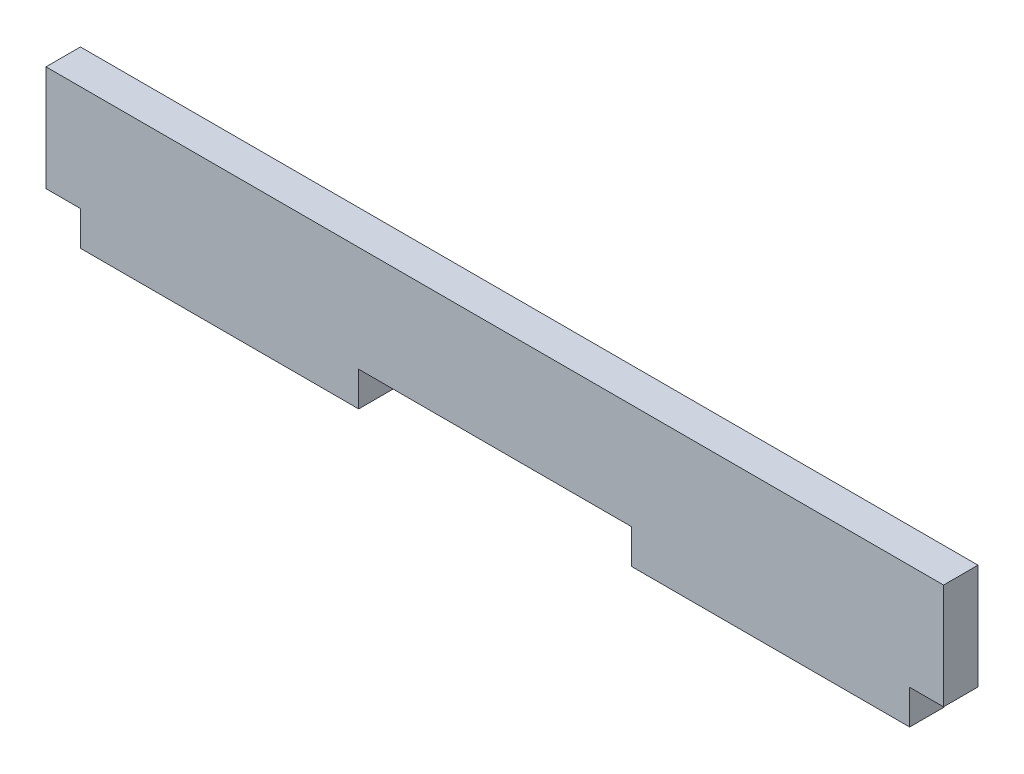
SolidWorks part; units mm, degrees
ref_plane "Front Plane" through (0, 0, 0) normal (0, 0, 1) x (1, 0, 0)
ref_plane "Top Plane" through (0, 0, 0) normal (0, 1, 0) x (1, 0, 0)
ref_plane "Right Plane" through (0, 0, 0) normal (1, 0, 0) x (0, 0, -1)
sketch "Sketch1" plane through (0, 0, 0) normal (0, 0, 1) x (1, 0, 0)
  line L0 (-12.6492, -4.7625) -> (12.7, -4.7625)
  line L1 (-41.275, 4.7625) -> (41.275, 4.7625)
  line L2 (-41.275, 4.7625) -> (-41.275, -4.7625)
  line L3 (-41.275, -4.7625) -> (-38.1, -4.7625)
  line L4 (41.275, 4.7625) -> (41.275, -4.7625)
  line L5 (-41.275, 4.7625) -> (41.275, -4.7625) construction
  line L6 (-41.275, -4.7625) -> (41.275, 4.7625) construction
  line L8 (-12.6492, -4.7625) -> (-12.6492, -7.9375)
  line L9 (-12.6492, -7.9375) -> (-38.1, -7.9375)
  line L10 (-38.1, -4.7625) -> (-38.1, -7.9375)
  line L12 (12.7, -4.7625) -> (12.7, -7.9375)
  line L13 (12.7, -7.9375) -> (38.1508, -7.9375)
  line L14 (38.1508, -4.7625) -> (38.1508, -7.9375)
  line L15 (38.1508, -4.7625) -> (41.275, -4.7625)
  point P0 (0, 0)
  point P14 (25.4254, -7.9375)
  point P15 (-25.3746, -7.9375)
  dimension "D1" = 9.525
  dimension "D2" = 82.55
  dimension "D3" = 3.175
  dimension "D4" = 25.4508
  dimension "D5" = 50.8
  dimension "D6" = 25.4508
  dimension "D7" = 12.7
extrude "Boss-Extrude1" add sketch "Sketch1" along normal mid plane 3.175
ref_plane "Plane1" through (0, 0, 1.5875) normal (0, 0, 1) x (1, 0, 0)
sketch "Sketch2" plane through (0, 0, 1.5875) normal (0, 0, 1) x (1, 0, 0)
  line L24 (38.2524, -4.8641) -> (41.3766, -4.8641)
  line L25 (41.3766, -4.8641) -> (41.3766, 4.8641)
  line L26 (41.3766, 4.8641) -> (-41.3766, 4.8641)
  line L27 (-41.3766, 4.8641) -> (-41.3766, -4.8641)
  line L28 (-41.3766, -4.8641) -> (-38.2016, -4.8641)
  line L29 (-38.2016, -4.8641) -> (-38.2016, -8.0391)
  line L30 (-38.2016, -8.0391) -> (-12.5476, -8.0391)
  line L31 (-12.5476, -8.0391) -> (-12.5476, -4.8641)
  line L32 (-12.5476, -4.8641) -> (12.5984, -4.8641)
  line L33 (12.5984, -4.8641) -> (12.5984, -8.0391)
  line L34 (12.5984, -8.0391) -> (38.2524, -8.0391)
  line L35 (38.2524, -8.0391) -> (38.2524, -4.8641)
  line L36 (38.2524, -4.8641) -> (41.3766, -4.8641)
  line L37 (41.3766, -4.8641) -> (41.3766, 4.8641)
  line L38 (41.3766, 4.8641) -> (-41.3766, 4.8641)
  line L39 (-41.3766, 4.8641) -> (-41.3766, -4.8641)
  line L40 (-41.3766, -4.8641) -> (-38.2016, -4.8641)
  line L41 (-38.2016, -4.8641) -> (-38.2016, -8.0391)
  line L42 (-38.2016, -8.0391) -> (-12.5476, -8.0391)
  line L43 (-12.5476, -8.0391) -> (-12.5476, -4.8641)
  line L44 (-12.5476, -4.8641) -> (12.5984, -4.8641)
  line L45 (12.5984, -4.8641) -> (12.5984, -8.0391)
  line L46 (12.5984, -8.0391) -> (38.2524, -8.0391)
  line L47 (38.2524, -8.0391) -> (38.2524, -4.8641)
  dimension "D1" = 0.1016
extrude "Boss-Extrude2" add sketch "Sketch2" against normal blind 3.175
